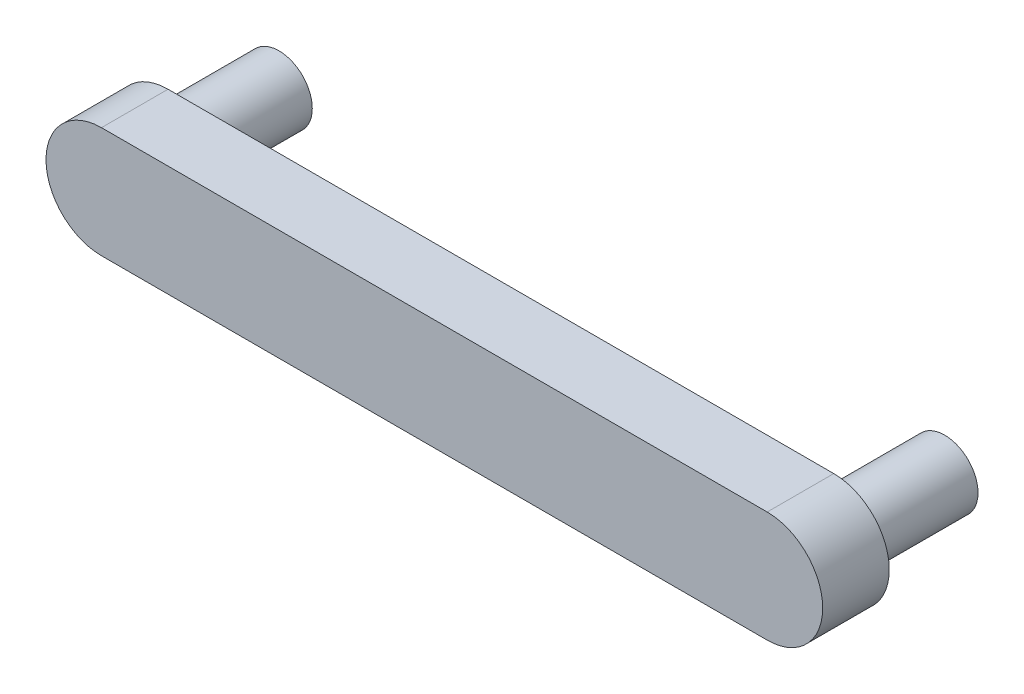
SolidWorks part; units mm, degrees
ref_plane "Front Plane" through (0, 0, 0) normal (0, 0, 1) x (1, 0, 0)
ref_plane "Top Plane" through (0, 0, 0) normal (0, 1, 0) x (1, 0, 0)
ref_plane "Right Plane" through (0, 0, 0) normal (1, 0, 0) x (0, 0, -1)
sketch "Sketch1" plane through (0, 0, 0) normal (0, 0, 1) x (1, 0, 0)
  line L1 (-15, -2.5) -> (15, -2.5)
  line L3 (-15, 2.5) -> (15, 2.5)
  line L5 (-15, -2.5) -> (15, 2.5) construction
  line L6 (-15, 2.5) -> (15, -2.5) construction
  arc A0 (15, 2.5) -> (15, -2.5) centre (15, 0) cw
  arc A1 (-15, 2.5) -> (-15, -2.5) centre (-15, 0) ccw
  point P0 (0, 0)
extrude "Boss-Extrude1" add sketch "Sketch1" along normal blind 3
sketch "Sketch3" plane through (0, 0, 0) normal (0, 0, 1) x (1, 0, 0)
  circle A0 centre (-15, 0) radius 1.5
  circle A1 centre (15, 0) radius 1.5
extrude "Boss-Extrude2" add sketch "Sketch3" against normal blind 5
